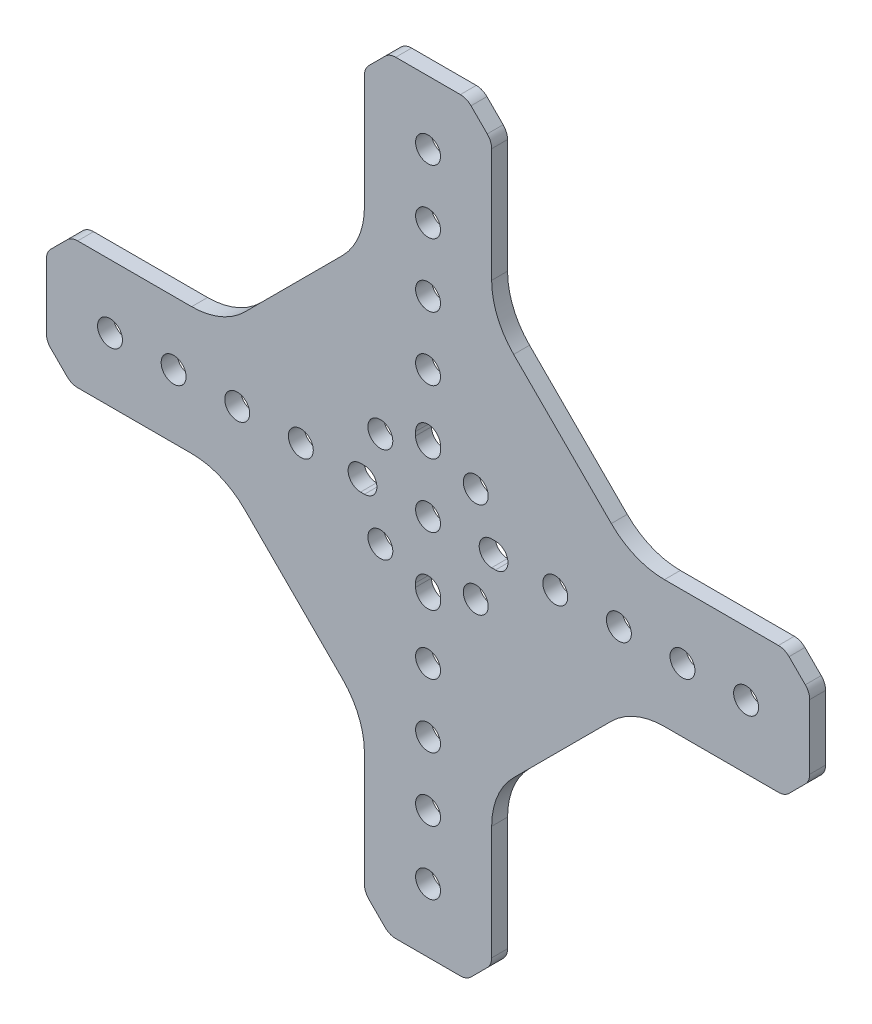
SolidWorks part; units mm, degrees
material "5052-H32"
ref_plane "Front Plane" through (0, 0, 0) normal (0, 0, 1) x (1, 0, 0)
ref_plane "Top Plane" through (0, 0, 0) normal (0, 1, 0) x (1, 0, 0)
ref_plane "Right Plane" through (0, 0, 0) normal (1, 0, 0) x (0, 0, -1)
ref_plane "Plane1" through (0, 0, 0) normal (0, 0, -1) x (-1, 0, 0)
sketch "Sketch1" plane through (0, 0, 0) normal (0, 0, -1) x (-1, 0, 0)
  line L0 (0, 15.1892) -> (0.7704, 15.1892)
  line L1 (0.7704, 10.2108) -> (0, 10.2108)
  line L2 (-26.1704, 15.1892) -> (-25.4, 15.1892)
  line L3 (-25.4, 10.2108) -> (-26.1704, 10.2108)
  line L4 (-15.1892, -0.7704) -> (-15.1892, 0)
  line L5 (-10.2108, 0) -> (-10.2108, -0.7704)
  line L6 (-10.2108, 26.1704) -> (-10.2108, 25.4)
  line L7 (-15.1892, 25.4) -> (-15.1892, 26.1704)
  line L8 (-59.8975, 25.4) -> (-82.6574, 25.4)
  line L9 (-84.7787, 24.5213) -> (-88.0213, 21.2787)
  line L10 (-88.9, 19.1574) -> (-88.9, 6.2426)
  line L11 (-88.0213, 4.1213) -> (-84.7787, 0.8787)
  line L12 (-82.6574, 0) -> (-59.8975, 0)
  line L13 (-49.2909, -4.3934) -> (-29.7934, -23.8909)
  line L14 (-25.4, -34.4975) -> (-25.4, -57.2574)
  line L15 (-24.5213, -59.3787) -> (-21.2787, -62.6213)
  line L16 (-19.1574, -63.5) -> (-6.2426, -63.5)
  line L17 (-4.1213, -62.6213) -> (-0.8787, -59.3787)
  line L18 (0, -57.2574) -> (0, -34.4975)
  line L19 (4.3934, -23.8909) -> (23.8909, -4.3934)
  line L20 (34.4975, 0) -> (57.2574, 0)
  line L21 (59.3787, 0.8787) -> (62.6213, 4.1213)
  line L22 (63.5, 6.2426) -> (63.5, 19.1574)
  line L23 (62.6213, 21.2787) -> (59.3787, 24.5213)
  line L24 (57.2574, 25.4) -> (34.4975, 25.4)
  line L25 (23.8909, 29.7934) -> (4.3934, 49.2909)
  line L26 (0, 59.8975) -> (0, 82.6574)
  line L27 (-0.8787, 84.7787) -> (-4.1213, 88.0213)
  line L28 (-6.2426, 88.9) -> (-19.1574, 88.9)
  line L29 (-21.2787, 88.0213) -> (-24.5213, 84.7787)
  line L30 (-25.4, 82.6574) -> (-25.4, 59.8975)
  line L31 (-29.7934, 49.2909) -> (-49.2909, 29.7934)
  circle A0 centre (-12.7, -12.7) radius 2.4892
  circle A1 centre (-12.7, -38.1) radius 2.4892
  circle A2 centre (-12.7, -25.4) radius 2.4892
  circle A3 centre (-12.7, -50.8) radius 2.4892
  arc A4 (0, 10.2108) -> (0, 15.1892) centre (0, 12.7) cw
  arc A5 (0.7704, 15.1892) -> (0.7704, 10.2108) centre (0.7704, 12.7) cw
  arc A6 (-25.4, 15.1892) -> (-25.4, 10.2108) centre (-25.4, 12.7) cw
  arc A7 (-26.1704, 10.2108) -> (-26.1704, 15.1892) centre (-26.1704, 12.7) cw
  circle A8 centre (-12.7, 12.7) radius 2.4892
  circle A9 centre (-63.5, 12.7) radius 2.4892
  circle A10 centre (-38.1, 12.7) radius 2.4892
  circle A11 centre (-76.2, 12.7) radius 2.4892
  circle A12 centre (-50.8, 12.7) radius 2.4892
  circle A13 centre (25.4, 12.7) radius 2.4892
  circle A14 centre (50.8, 12.7) radius 2.4892
  circle A15 centre (12.7, 12.7) radius 2.4892
  circle A16 centre (38.1, 12.7) radius 2.4892
  arc A17 (-15.1892, 0) -> (-10.2108, 0) centre (-12.7, 0) cw
  arc A18 (-10.2108, -0.7704) -> (-15.1892, -0.7704) centre (-12.7, -0.7704) cw
  circle A19 centre (-12.7, 50.8) radius 2.4892
  circle A20 centre (-12.7, 63.5) radius 2.4892
  circle A21 centre (-12.7, 38.1) radius 2.4892
  circle A22 centre (-12.7, 76.2) radius 2.4892
  arc A23 (-10.2108, 25.4) -> (-15.1892, 25.4) centre (-12.7, 25.4) cw
  arc A24 (-15.1892, 26.1704) -> (-10.2108, 26.1704) centre (-12.7, 26.1704) cw
  circle A25 centre (-3.175, 3.175) radius 2.4892
  circle A26 centre (-22.225, 3.175) radius 2.4892
  circle A27 centre (-22.225, 22.225) radius 2.4892
  circle A28 centre (-3.175, 22.225) radius 2.4892
  arc A29 (-49.2909, 29.7934) -> (-59.8975, 25.4) centre (-59.8975, 40.4) cw
  arc A30 (-82.6574, 25.4) -> (-84.7787, 24.5213) centre (-82.6574, 22.4) ccw
  arc A31 (-88.0213, 21.2787) -> (-88.9, 19.1574) centre (-85.9, 19.1574) ccw
  arc A32 (-88.9, 6.2426) -> (-88.0213, 4.1213) centre (-85.9, 6.2426) ccw
  arc A33 (-84.7787, 0.8787) -> (-82.6574, 0) centre (-82.6574, 3) ccw
  arc A34 (-59.8975, 0) -> (-49.2909, -4.3934) centre (-59.8975, -15) cw
  arc A35 (-29.7934, -23.8909) -> (-25.4, -34.4975) centre (-40.4, -34.4975) cw
  arc A36 (-25.4, -57.2574) -> (-24.5213, -59.3787) centre (-22.4, -57.2574) ccw
  arc A37 (-21.2787, -62.6213) -> (-19.1574, -63.5) centre (-19.1574, -60.5) ccw
  arc A38 (-6.2426, -63.5) -> (-4.1213, -62.6213) centre (-6.2426, -60.5) ccw
  arc A39 (-0.8787, -59.3787) -> (0, -57.2574) centre (-3, -57.2574) ccw
  arc A40 (0, -34.4975) -> (4.3934, -23.8909) centre (15, -34.4975) cw
  arc A41 (23.8909, -4.3934) -> (34.4975, 0) centre (34.4975, -15) cw
  arc A42 (57.2574, 0) -> (59.3787, 0.8787) centre (57.2574, 3) ccw
  arc A43 (62.6213, 4.1213) -> (63.5, 6.2426) centre (60.5, 6.2426) ccw
  arc A44 (63.5, 19.1574) -> (62.6213, 21.2787) centre (60.5, 19.1574) ccw
  arc A45 (59.3787, 24.5213) -> (57.2574, 25.4) centre (57.2574, 22.4) ccw
  arc A46 (34.4975, 25.4) -> (23.8909, 29.7934) centre (34.4975, 40.4) cw
  arc A47 (4.3934, 49.2909) -> (0, 59.8975) centre (15, 59.8975) cw
  arc A48 (0, 82.6574) -> (-0.8787, 84.7787) centre (-3, 82.6574) ccw
  arc A49 (-4.1213, 88.0213) -> (-6.2426, 88.9) centre (-6.2426, 85.9) ccw
  arc A50 (-19.1574, 88.9) -> (-21.2787, 88.0213) centre (-19.1574, 85.9) ccw
  arc A51 (-24.5213, 84.7787) -> (-25.4, 82.6574) centre (-22.4, 82.6574) ccw
  arc A52 (-25.4, 59.8975) -> (-29.7934, 49.2909) centre (-40.4, 59.8975) cw
  dimension "D1" = 4.9784
  dimension "D2" = 4.9784
  dimension "D3" = 4.9784
  dimension "D4" = 4.9784
  dimension "D5" = 4.9784
  dimension "D6" = 4.9784
  dimension "D7" = 4.9784
  dimension "D8" = 4.9784
  dimension "D9" = 4.9784
  dimension "D10" = 4.9784
  dimension "D11" = 4.9784
  dimension "D12" = 4.9784
  dimension "D13" = 4.9784
  dimension "D14" = 4.9784
  dimension "D15" = 4.9784
  dimension "D16" = 4.9784
  dimension "D17" = 4.9784
  dimension "D18" = 4.9784
  dimension "D19" = 4.9784
  dimension "D20" = 4.9784
  dimension "D21" = 4.9784
  dimension "D22" = 2.4892
  dimension "D23" = 2.4892
  dimension "D24" = 2.4892
  dimension "D25" = 2.4892
  dimension "D26" = 2.4892
  dimension "D27" = 2.4892
  dimension "D28" = 2.4892
  dimension "D29" = 2.4892
  dimension "D30" = 12.7
  dimension "D31" = 25.4
  dimension "D32" = 38.1
  dimension "D33" = 50.8
  dimension "D34" = 66.675
  dimension "D35" = 85.725
  dimension "D36" = 101.6
  dimension "D37" = 114.3
  dimension "D38" = 127
  dimension "D39" = 139.7
  dimension "D40" = 12.7
  dimension "D41" = 25.4
  dimension "D42" = 38.1
  dimension "D43" = 50.8
  dimension "D44" = 66.675
  dimension "D45" = 85.725
  dimension "D46" = 101.6
  dimension "D47" = 114.3
  dimension "D48" = 127
  dimension "D49" = 139.7
extrude "Boss-Extrude1" add sketch "Sketch1" against normal blind 3.175
